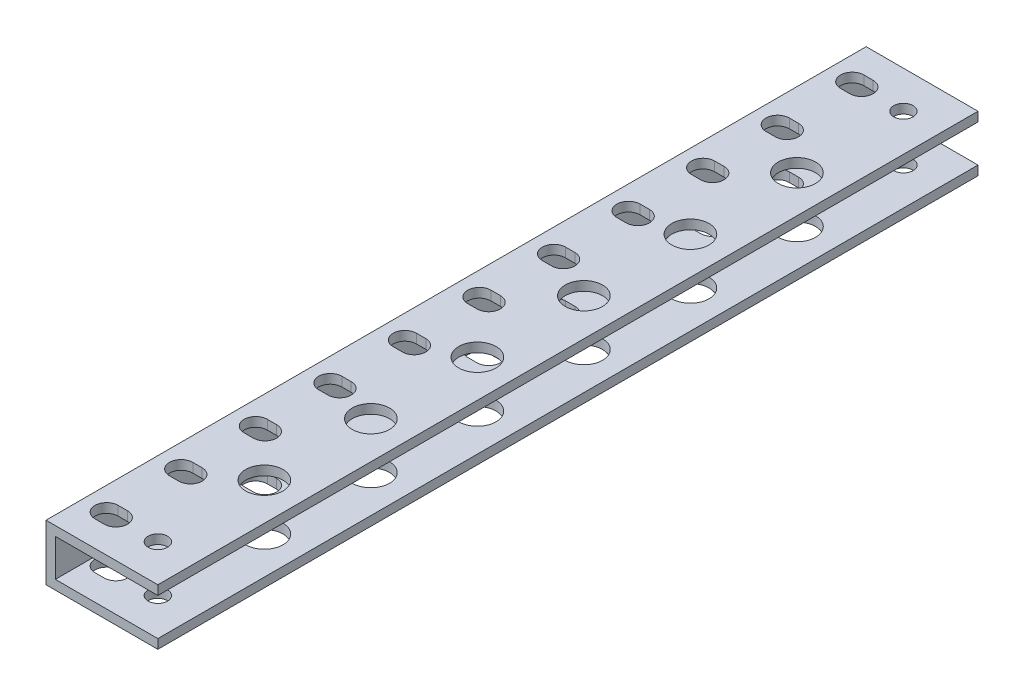
SolidWorks part; units mm, degrees
material "6061-T6 (SS)"
ref_plane "Front Plane" through (0, 0, 0) normal (0, 0, 1) x (1, 0, 0)
ref_plane "Top Plane" through (0, 0, 0) normal (0, 1, 0) x (1, 0, 0)
ref_plane "Right Plane" through (0, 0, 0) normal (1, 0, 0) x (0, 0, -1)
sketch "Sketch1" plane through (0, 0, 0) normal (0, 1, 0) x (1, 0, 0)
  line L0 (7.9375, 266.7) -> (11.1125, 266.7) construction
  line L1 (0, 0) -> (38.1, 0)
  line L2 (0, 0) -> (0, 279.4)
  line L3 (0, 279.4) -> (38.1, 279.4)
  line L4 (38.1, 0) -> (38.1, 279.4)
  line L5 (9.525, 266.7) -> (9.525, 12.7) construction
  line L6 (7.9375, 270.6687) -> (11.1125, 270.6687)
  line L7 (7.9375, 262.7312) -> (11.1125, 262.7312)
  line L8 (7.9375, 237.3312) -> (11.1125, 237.3312)
  line L9 (7.9375, 245.2688) -> (11.1125, 245.2688)
  line L10 (7.9375, 241.3) -> (11.1125, 241.3) construction
  line L11 (7.9375, 211.9312) -> (11.1125, 211.9312)
  line L12 (7.9375, 219.8688) -> (11.1125, 219.8688)
  line L13 (7.9375, 215.9) -> (11.1125, 215.9) construction
  line L14 (7.9375, 186.5312) -> (11.1125, 186.5312)
  line L15 (7.9375, 194.4688) -> (11.1125, 194.4688)
  line L16 (7.9375, 190.5) -> (11.1125, 190.5) construction
  line L17 (7.9375, 161.1312) -> (11.1125, 161.1312)
  line L18 (7.9375, 169.0688) -> (11.1125, 169.0688)
  line L19 (7.9375, 165.1) -> (11.1125, 165.1) construction
  line L20 (7.9375, 135.7312) -> (11.1125, 135.7312)
  line L21 (7.9375, 143.6688) -> (11.1125, 143.6688)
  line L22 (7.9375, 139.7) -> (11.1125, 139.7) construction
  line L23 (7.9375, 110.3312) -> (11.1125, 110.3312)
  line L24 (7.9375, 118.2688) -> (11.1125, 118.2688)
  line L25 (7.9375, 114.3) -> (11.1125, 114.3) construction
  line L26 (7.9375, 84.9312) -> (11.1125, 84.9312)
  line L27 (7.9375, 92.8688) -> (11.1125, 92.8688)
  line L28 (7.9375, 88.9) -> (11.1125, 88.9) construction
  line L29 (7.9375, 59.5312) -> (11.1125, 59.5312)
  line L30 (7.9375, 67.4688) -> (11.1125, 67.4688)
  line L31 (7.9375, 63.5) -> (11.1125, 63.5) construction
  line L32 (7.9375, 34.1312) -> (11.1125, 34.1312)
  line L33 (7.9375, 42.0688) -> (11.1125, 42.0688)
  line L34 (7.9375, 38.1) -> (11.1125, 38.1) construction
  line L35 (7.9375, 8.7312) -> (11.1125, 8.7312)
  line L36 (7.9375, 16.6688) -> (11.1125, 16.6688)
  line L37 (7.9375, 12.7) -> (11.1125, 12.7) construction
  arc A19 (7.9375, 270.6687) -> (7.9375, 262.7312) centre (7.9375, 266.7) ccw
  arc A20 (11.1125, 262.7312) -> (11.1125, 270.6687) centre (11.1125, 266.7) ccw
  arc A21 (7.9375, 245.2688) -> (7.9375, 237.3312) centre (7.9375, 241.3) ccw
  arc A22 (11.1125, 237.3312) -> (11.1125, 245.2688) centre (11.1125, 241.3) ccw
  arc A23 (7.9375, 219.8688) -> (7.9375, 211.9312) centre (7.9375, 215.9) ccw
  arc A24 (11.1125, 211.9312) -> (11.1125, 219.8688) centre (11.1125, 215.9) ccw
  arc A25 (7.9375, 194.4688) -> (7.9375, 186.5312) centre (7.9375, 190.5) ccw
  arc A26 (11.1125, 186.5312) -> (11.1125, 194.4688) centre (11.1125, 190.5) ccw
  arc A27 (7.9375, 169.0688) -> (7.9375, 161.1312) centre (7.9375, 165.1) ccw
  arc A28 (11.1125, 161.1312) -> (11.1125, 169.0688) centre (11.1125, 165.1) ccw
  arc A29 (7.9375, 143.6688) -> (7.9375, 135.7312) centre (7.9375, 139.7) ccw
  arc A30 (11.1125, 135.7312) -> (11.1125, 143.6688) centre (11.1125, 139.7) ccw
  arc A31 (7.9375, 118.2688) -> (7.9375, 110.3312) centre (7.9375, 114.3) ccw
  arc A32 (11.1125, 110.3312) -> (11.1125, 118.2688) centre (11.1125, 114.3) ccw
  arc A33 (7.9375, 92.8688) -> (7.9375, 84.9312) centre (7.9375, 88.9) ccw
  arc A34 (11.1125, 84.9312) -> (11.1125, 92.8688) centre (11.1125, 88.9) ccw
  arc A35 (7.9375, 67.4688) -> (7.9375, 59.5312) centre (7.9375, 63.5) ccw
  arc A36 (11.1125, 59.5312) -> (11.1125, 67.4688) centre (11.1125, 63.5) ccw
  arc A37 (7.9375, 42.0688) -> (7.9375, 34.1312) centre (7.9375, 38.1) ccw
  arc A38 (11.1125, 34.1312) -> (11.1125, 42.0688) centre (11.1125, 38.1) ccw
  arc A39 (7.9375, 16.6688) -> (7.9375, 8.7312) centre (7.9375, 12.7) ccw
  arc A40 (11.1125, 8.7312) -> (11.1125, 16.6688) centre (11.1125, 12.7) ccw
  point P8 (9.525, 266.7)
  point P13 (9.525, 241.3)
  point P20 (9.525, 215.9)
  point P28 (9.525, 190.5)
  point P47 (9.525, 165.1)
  point P54 (9.525, 139.7)
  point P61 (9.525, 114.3)
  point P68 (9.525, 88.9)
  point P75 (9.525, 63.5)
  point P82 (9.525, 38.1)
  point P89 (9.525, 12.7)
  dimension "D3" = 11
  dimension "D1" = 38.1
  dimension "D2" = 279.4
  dimension "D4" = 9.525
  dimension "D5" = 12.7
  dimension "D7" = 3.175
  dimension "D8" = 25.4
  dimension "D6" = 7.9375
extrude "Boss-Extrude1" add sketch "Sketch1" along normal blind 19.05
sketch "Sketch2" plane through (0, 19.05, 0) normal (0, 1, 0) x (1, 0, 0)
  line L0 (38.1, 0) -> (38.1, 279.4) construction
  line L1 (38.1, 279.4) -> (0, 279.4) construction
  circle A0 centre (25.4, 266.7) radius 6.35
  circle A1 centre (25.4, 230.4143) radius 6.35
  circle A2 centre (25.4, 194.1286) radius 6.35
  circle A3 centre (25.4, 157.8429) radius 6.35
  circle A4 centre (25.4, 121.5571) radius 6.35
  circle A5 centre (25.4, 85.2714) radius 6.35
  circle A6 centre (25.4, 48.9857) radius 6.35
  circle A7 centre (25.4, 12.7) radius 6.35
  circle A8 centre (25.4, 266.7) radius 3.302
  circle A9 centre (25.4, 12.7) radius 3.302
  dimension "D1" = 12.7
  dimension "D5" = 6.604
  dimension "D2" = 12.7
  dimension "D3" = 12.7
  dimension "D6" = 36.2857
  dimension "D4" = 8
extrude "Cut-Extrude1" cut sketch "Sketch2" against normal through all contours A8 | A1 | A2 | A3 | A4 | A5 | A9 | A6 | A0
sketch "Sketch3" plane through (0, 0, 0) normal (0, 0, 1) x (1, 0, 0)
  line L1 (38.1, 15.875) -> (3.175, 15.875)
  line L2 (38.1, 15.875) -> (38.1, 3.175)
  line L3 (38.1, 3.175) -> (3.175, 3.175)
  line L4 (0, 0) -> (38.1, 0)
  line L5 (38.1, 0) -> (38.1, 19.05)
  line L6 (38.1, 19.05) -> (0, 19.05)
  line L7 (0, 19.05) -> (0, 0)
  line L8 (0, 0) -> (38.1, 0)
  line L9 (38.1, 0) -> (38.1, 19.05)
  line L10 (38.1, 19.05) -> (0, 19.05)
  line L11 (0, 19.05) -> (0, 0)
  line L12 (3.175, 15.875) -> (3.175, 3.175)
  point P8 (38.1, 9.525)
  line M10 (38.1, 0) -> (38.1, 19.05)
  dimension "D2" = 12.7
  dimension "D3" = 34.925
  dimension "D1" = 0
extrude "Cut-Extrude2" cut sketch "Sketch3" against normal blind 330.2 contours L1 L12 L3 M10
